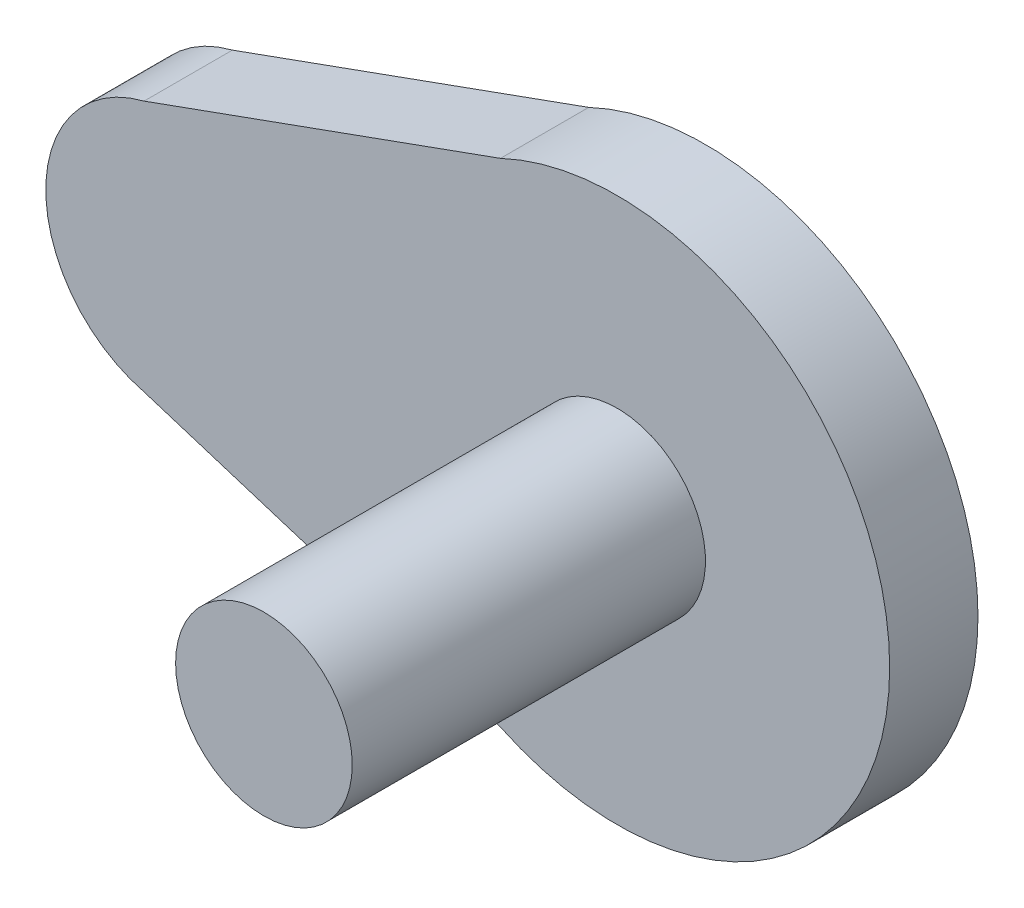
SolidWorks part; units mm, degrees
ref_plane "Front Plane" through (0, 0, 0) normal (0, 0, 1) x (1, 0, 0)
ref_plane "Top Plane" through (0, 0, 0) normal (0, 1, 0) x (1, 0, 0)
ref_plane "Right Plane" through (0, 0, 0) normal (1, 0, 0) x (0, 0, -1)
sketch "Sketch1" plane through (0, 0, 0) normal (0, 0, 1) x (1, 0, 0)
  line L0 (0, 14.2595) -> (20.177, 21.5401)
  line L1 (0, 0) -> (20.177, -6.346)
  line L2 (16.4042, 32.7501) -> (16.4042, -23.8766) construction
  line L3 (0, 14.2595) -> (0, 0) construction
  arc A0 (0, 0) -> (0, 14.2595) centre (1.7857, 7.1298) cw
  arc A3 (20.177, -6.346) -> (20.177, 21.5401) centre (26.7857, 7.5971) ccw
  dimension "D2" = 15.43
  dimension "D3" = 7.35
  dimension "D1" = 25
extrude "Boss-Extrude1" add sketch "Sketch1" along normal blind 5
sketch "Sketch2" plane through (0, 0, 5) normal (0, 0, 1) x (1, 0, 0)
  circle A0 centre (26.7857, 7.5971) radius 5
  dimension "D1" = 10
extrude "Boss-Extrude2" add sketch "Sketch2" along normal blind 20
sketch "Sketch3" plane through (0, 0, 0) normal (0, 0, -1) x (-1, 0, 0)
  circle A0 centre (-1.7857, 7.1298) radius 2.5
  dimension "D1" = 5
extrude "Boss-Extrude3" add sketch "Sketch3" along normal blind 5
